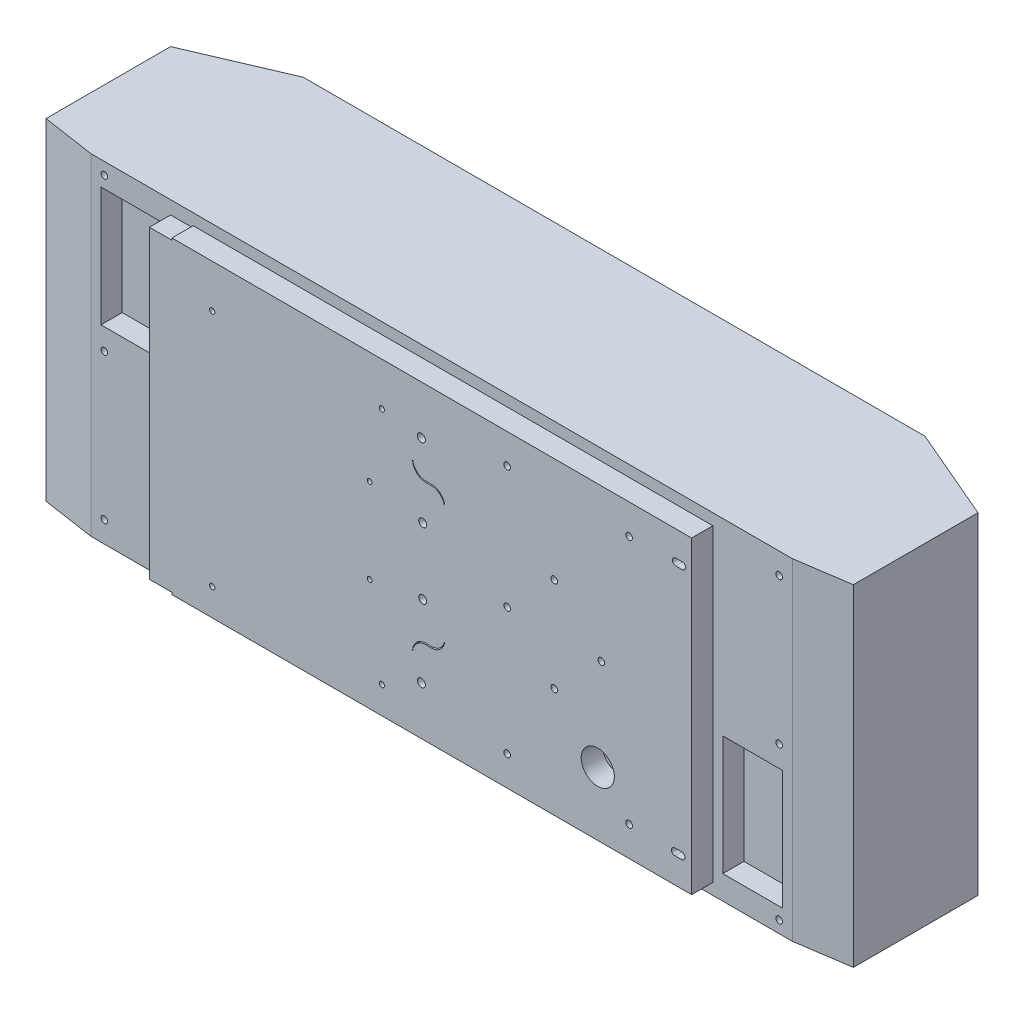
SolidWorks part; units mm, degrees
ref_plane "前视基准面" through (0, 0, 0) normal (0, 0, 1) x (1, 0, 0)
ref_plane "上视基准面" through (0, 0, 0) normal (0, 1, 0) x (1, 0, 0)
ref_plane "右视基准面" through (0, 0, 0) normal (1, 0, 0) x (0, 0, -1)
sketch "草图1" plane through (0, 0, 0) normal (0, 0, 1) x (1, 0, 0)
  line L0 (-6.6, 116.5) -> (-188.13, 116.5)
  line L1 (-188.13, -118) -> (-188.13, -116.5)
  line L2 (-6.6, -116.5) -> (-6.6, -118)
  line L3 (-6.6, -118) -> (-188.13, -118)
  line L4 (3.4, -52.5) -> (7.6, -52.5)
  line L5 (-188.13, 116.5) -> (-188.13, 118)
  line L6 (-6.6, 118) -> (-6.6, 116.5)
  line L7 (-188.13, -116.5) -> (-6.6, -116.5)
  line L8 (-6.6, -116.5) -> (-6.6, -62.5)
  line L9 (-188.13, -115) -> (-188.13, -116.5)
  line L10 (-205.13, -115) -> (-188.13, -115)
  line L11 (-205.13, 115) -> (-205.13, -115)
  line L12 (-188.13, 115) -> (-205.13, 115)
  line L13 (-188.13, 116.5) -> (-188.13, 115)
  line L14 (-6.6, 62.5) -> (-6.6, 116.5)
  line L15 (7.6, 52.5) -> (3.4, 52.5)
  line L16 (-188.13, 118) -> (-6.6, 118)
  line L17 (17.6, -42.5) -> (17.6, 42.5)
  line L18 (203.87, -116.5) -> (203.87, -118)
  line L19 (-6.6, -118) -> (-6.6, -116.5)
  line L20 (-6.6, 118) -> (203.87, 118)
  line L21 (-6.6, 118) -> (-6.6, 116.5)
  line L22 (203.87, 118) -> (203.87, 116.5)
  line L23 (-6.6, 116.5) -> (-6.6, 63.5)
  line L24 (3.4, 53.5) -> (7.6, 53.5)
  line L25 (203.87, -116.5) -> (203.87, 116.5)
  line L26 (17.6, 43.5) -> (17.6, -43.5)
  line L27 (203.87, 116.5) -> (-6.6, 116.5)
  line L28 (196.3, -92.28) -> (191.2, -92.28)
  line L29 (7.6, -53.5) -> (3.4, -53.5)
  line L30 (203.87, -118) -> (-6.6, -118)
  line L31 (191.2, -97.38) -> (196.3, -97.38)
  line L32 (196.9328, 97.3711) -> (191.8328, 97.3711)
  line L33 (-6.6, -116.5) -> (203.87, -116.5)
  line L34 (191.8328, 92.2711) -> (196.9328, 92.2711)
  line L35 (-6.6, -63.5) -> (-6.6, -116.5)
  line L36 (-205.13, 0) -> (203.87, 0) construction
  line L37 (0, 164.7602) -> (0, -124.0936) construction
  arc A0 (7.6, -52.5) -> (17.6, -42.5) centre (7.6, -42.5) ccw
  circle A1 centre (1, -25) radius 3
  circle A2 centre (1, 25) radius 3
  circle A3 centre (-29.765, -96) radius 2
  circle A4 centre (-157.765, -96) radius 2
  circle A5 centre (-157.765, 84) radius 2
  circle A6 centre (-29.765, 84) radius 2
  arc A7 (3.4, -52.5) -> (-6.6, -62.5) centre (3.4, -62.5) ccw
  circle A8 centre (-39, 32) radius 1.8
  circle A9 centre (-39, -32) radius 1.8
  arc A10 (-6.6, 62.5) -> (3.4, 52.5) centre (3.4, 62.5) ccw
  arc A11 (17.6, 42.5) -> (7.6, 52.5) centre (7.6, 42.5) ccw
  arc A12 (191.8328, 97.3711) -> (191.8328, 92.2711) centre (191.8328, 94.8211) ccw
  circle A13 centre (156.735, -94) radius 2.5
  circle A14 centre (0, 80) radius 3
  arc A15 (17.6, 43.5) -> (7.6, 53.5) centre (7.6, 43.5) ccw
  circle A16 centre (100.2546, -33.6765) radius 2.5
  circle A17 centre (100.2546, 37.3235) radius 2.5
  circle A18 centre (0, -80) radius 3
  circle A19 centre (64.735, 94) radius 2.5
  arc A20 (-6.6, 63.5) -> (3.4, 53.5) centre (3.4, 63.5) ccw
  arc A21 (196.3, -97.38) -> (196.3, -92.28) centre (196.3, -94.83) ccw
  circle A22 centre (64.735, -94) radius 2.5
  circle A23 centre (135.7546, 1.8235) radius 2.5
  arc A24 (191.2, -92.28) -> (191.2, -97.38) centre (191.2, -94.83) ccw
  circle A25 centre (64.7546, 1.8235) radius 2.5
  circle A26 centre (156.735, 94) radius 2.5
  arc A27 (7.6, -53.5) -> (17.6, -43.5) centre (7.6, -43.5) ccw
  arc A28 (196.9328, 92.2711) -> (196.9328, 97.3711) centre (196.9328, 94.8211) ccw
  arc A29 (3.4, -53.5) -> (-6.6, -63.5) centre (3.4, -63.5) ccw
  circle A30 centre (133.0743, -68.6633) radius 12.5
extrude "凸台-拉伸1" add sketch "草图1" against normal blind 16 separate body contours L17 A11 L15 A10 L14 L0 L13 L12 L11 L10 L9 L7 L8 A7 L4 A0 A1 A2 A3 A4 A5 A6 A8 A9 | L29 A29 L8 L33 L25 L27 L14 A20 L24 A15 L26 L17 A27 A30 A28 L34 A12 L32 A26 A25 A24 L28 A21 L31 A23 A22 A19 A18 A17 A16 A14 A13
ref_plane "基准面2" through (0, 0, 20) normal (0, 0, 1) x (1, 0, 0)
sketch "草图5" plane through (0, 0, 20) normal (0, 0, 1) x (1, 0, 0)
  line L0 (156.735, 150) -> (156.735, -150)
  line L1 (-157.765, 150) -> (-157.765, -150)
  line L2 (-205.13, 0) -> (203.87, 0) construction
  circle A0 centre (-157.765, -96) radius 2 construction
  circle A1 centre (-157.765, -96) radius 2
  circle A2 centre (156.735, -94) radius 2.5 construction
  circle A3 centre (156.735, 94) radius 2.5 construction
  circle A4 centre (-157.765, 84) radius 2 construction
  circle A5 centre (156.735, -94) radius 2.5
  circle A6 centre (156.735, 94) radius 2.5
  circle A7 centre (-157.765, 84) radius 2
  dimension "D1" = 300
  dimension "D2" = 300
  dimension "D3" = 150
  dimension "D4" = 150
sketch "草图9" plane through (0, 0, -16) normal (0, 0, -1) x (-1, 0, 0)
  line L0 (265.13, 0) -> (-263.87, 0) construction
  line L1 (265.13, 125) -> (-263.87, 125)
  line L2 (265.13, -125) -> (-263.87, -125)
  line L4 (-203.87, -116.5) -> (-203.87, 116.5) construction
  line L5 (205.13, 115) -> (205.13, -115) construction
  line L6 (205.13, 115) -> (205.13, -115) construction
  line L7 (-263.87, -125) -> (-263.87, 125)
  line L8 (265.13, 125) -> (265.13, -125)
  line L9 (265.13, 115) -> (265.13, -115) construction
  line L10 (409.894, -125) -> (-442.8346, -125) construction
  line L11 (409.894, 0) -> (-442.8346, 0) construction
  line L12 (409.894, 125) -> (-442.8346, 125) construction
  dimension "D3" = 60
  dimension "D1" = 125
  dimension "D2" = 125
  dimension "D4" = 60
extrude "凸台-拉伸2" add sketch "草图9" along normal blind 16 separate body contours L1 L7 L2 L8
sketch "草图10" plane through (0, 0, -16) normal (0, 0, 1) x (1, 0, 0)
  line L0 (-294.191, 0) -> (297.0153, 0) construction
  line L1 (-212.63, 17) -> (-212.63, 107)
  line L2 (-265.13, -17) -> (263.87, -17)
  line L3 (211.37, -17) -> (256.37, -17)
  line L4 (-235.13, 17) -> (-235.13, 107) construction
  line L5 (-265.13, -107) -> (263.87, -107)
  line L6 (211.37, -107) -> (256.37, -107)
  line L7 (-257.63, 17) -> (-257.63, 107)
  line L8 (-265.13, 107) -> (263.87, 107)
  line L9 (-257.63, 107) -> (-212.63, 107)
  line L10 (-265.13, 125) -> (-265.13, -125) construction
  line L11 (-265.13, 17) -> (263.87, 17)
  line L12 (-257.63, 17) -> (-212.63, 17)
  line L17 (233.87, -125) -> (233.87, 125)
  line L18 (233.87, -107) -> (233.87, -17) construction
  line L20 (256.37, -107) -> (256.37, -17)
  line L21 (211.37, -107) -> (211.37, -17)
  dimension "D5" = 30
  dimension "D7" = 22.5
  dimension "D8" = 22.5
  dimension "D1" = 108
  dimension "D2" = 18
  dimension "D3" = 18
  dimension "D4" = 108
  dimension "D6" = 30
  dimension "D9" = 22.5
  dimension "D10" = 22.5
extrude "切除-拉伸3" cut sketch "草图10" against normal through all
sketch "草图12" plane through (0, -125, 0) normal (0, -1, 0) x (1, 0, 0)
  line L0 (263.87, -32) -> (303.87, -32)
  line L1 (303.87, -32) -> (303.87, -22)
  line L2 (303.87, -22) -> (263.87, -16)
  line L3 (-265.13, -32) -> (-305.13, -32)
  line L4 (-305.13, -32) -> (-305.13, -22)
  line L5 (-305.13, -22) -> (-265.13, -16)
  line L6 (-265.13, -32) -> (-265.13, -16)
  line L7 (263.87, -16) -> (263.87, -32)
  dimension "D1" = 40
  dimension "D2" = 10
  dimension "D3" = 40
  dimension "D4" = 10
extrude "凸台-拉伸3" add sketch "草图12" against normal up to surface (250 mm away) up to face at (-0.63, 125, -24)
sketch "草图13" plane through (0, 0, -16) normal (0, 0, 1) x (1, 0, 0)
  line L1 (211.37, -107) -> (256.37, -107) construction
  line L2 (-265.13, 125) -> (263.87, 125) construction
  line L3 (256.37, -17) -> (211.37, -17) construction
  line L5 (263.87, -125) -> (263.87, 125) construction
  line L6 (-265.13, -125) -> (263.87, -125) construction
  line L7 (-257.63, 17) -> (-212.63, 17) construction
  line L8 (-205.13, 115) -> (-205.13, -115) construction
  line L9 (-205.13, 115) -> (-205.13, -115) construction
  line L10 (-205.13, 0) -> (-277.1127, 0) construction
  circle A0 centre (253.87, 109) radius 2.5
  circle A1 centre (253.87, -1) radius 2.5
  circle A2 centre (-255.13, 1) radius 2.5
  circle A3 centre (-255.13, -109) radius 2.5
  circle A4 centre (-255.13, 116) radius 2.5
  circle A5 centre (253.87, -116) radius 2.5
  dimension "D1" = 5
  dimension "D2" = 5
  dimension "D3" = 16
  dimension "D4" = 16
  dimension "D5" = 5
  dimension "D6" = 5
  dimension "D7" = 16
  dimension "D8" = 16
  dimension "D10" = 5
  dimension "D11" = 9
  dimension "D12" = 5
  dimension "D13" = 9
  dimension "D14" = 110
  dimension "D15" = 10
extrude "切除-拉伸4" cut sketch "草图13" against normal through all
sketch "草图16" plane through (0, 0, -32) normal (0, 0, -1) x (-1, 0, 0)
  line L1 (-303.87, 125) -> (305.13, 125)
  line L2 (-303.87, 125) -> (-303.87, -125)
  line L3 (-303.87, -125) -> (305.13, -125)
  line L4 (305.13, 125) -> (305.13, -125)
extrude "凸台-拉伸5" add sketch "草图16" along normal blind 114
sketch "草图17" plane through (0, 125, 0) normal (0, 1, 0) x (1, 0, 0)
  line L0 (303.87, 116) -> (233.87, 146)
  line L1 (303.87, 146) -> (303.87, 22) construction
  line L2 (-305.13, 146) -> (303.87, 146) construction
  line L3 (233.87, 146) -> (303.87, 146)
  line L4 (303.87, 146) -> (303.87, 116)
  line L5 (-0.63, 146) -> (-0.63, -49.9887) construction
  line L6 (-305.13, 146) -> (-305.13, 116)
  line L7 (-235.13, 146) -> (-305.13, 146)
  line L8 (-305.13, 116) -> (-235.13, 146)
  dimension "D1" = 30
  dimension "D2" = 70
extrude "切除-拉伸5" cut sketch "草图17" against normal through all
sketch "草图18" plane through (0, 125, 0) normal (0, 1, 0) x (1, 0, 0)
  line L0 (0, -84.2094) -> (0, 67.2678) construction
  line L1 (-265.13, 16) -> (263.87, 16) construction
  circle A0 centre (180, 106) radius 10
  circle A1 centre (-180, 106) radius 10
  dimension "D1" = 20
  dimension "D3" = 90
  dimension "D2" = 180
sketch "草图19" plane through (0, -125, 0) normal (0, -1, 0) x (1, 0, 0)
  circle A0 centre (-180, -106) radius 10 construction
  circle A1 centre (-180, -106) radius 10
  circle A2 centre (180, -106) radius 10 construction
  circle A3 centre (180, -106) radius 10
